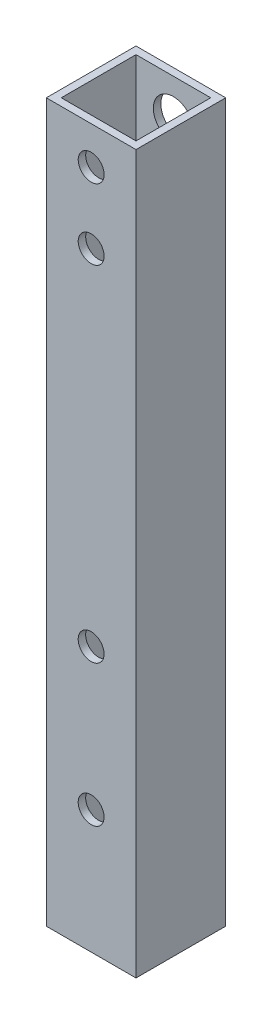
SolidWorks part; units mm, degrees
material "6063-T5"
ref_plane "Front Plane" through (0, 0, 0) normal (0, 0, 1) x (1, 0, 0)
ref_plane "Top Plane" through (0, 0, 0) normal (0, 1, 0) x (1, 0, 0)
ref_plane "Right Plane" through (0, 0, 0) normal (1, 0, 0) x (0, 0, -1)
sketch "Sketch1" plane through (0, 0, 0) normal (0, 1, 0) x (1, 0, 0)
  line L0 (1.5875, 1.5875) -> (17.4625, 1.5875)
  line L5 (0, 0) -> (19.05, 0)
  line L6 (0, 0) -> (0, 19.05)
  line L7 (0, 19.05) -> (19.05, 19.05)
  line L8 (19.05, 0) -> (19.05, 19.05)
  line L9 (17.4625, 1.5875) -> (17.4625, 17.4625)
  line L10 (1.5875, 17.4625) -> (17.4625, 17.4625)
  line L11 (1.5875, 1.5875) -> (1.5875, 17.4625)
  dimension "D1" = 19.05
  dimension "D2" = 19.05
  dimension "D3" = 1.5875
extrude "Boss-Extrude1" add sketch "Sketch1" along normal blind 914.4
sketch "Sketch2" plane through (0, 0, 0) normal (0, 0, 1) x (1, 0, 0)
  line L0 (0, 914.4) -> (19.05, 914.4) construction
  circle A0 centre (9.525, 906.4) radius 2.75
  circle A1 centre (9.525, 891.4) radius 2.75
  dimension "D3" = 5.5
  dimension "D4" = 5.5
  dimension "D1" = 8
  dimension "D2" = 15
extrude "Cut-Extrude1" cut sketch "Sketch2" against normal through all
sketch "Sketch3" plane through (0, 0, -19.05) normal (0, 0, -1) x (-1, 0, 0)
  circle A0 centre (-9.525, 906.4) radius 4.255
  circle A1 centre (-9.525, 891.4) radius 4.255
  dimension "D1" = 8.51
  dimension "D2" = 8.51
extrude "Cut-Extrude2" cut sketch "Sketch3" against normal up to next
sketch "Sketch4" plane through (0, 0, 0) normal (0, 0, 1) x (1, 0, 0)
  line L0 (19.05, 914.4) -> (19.05, 0) construction
  line L1 (0, 0) -> (19.05, 0)
  line L2 (0, 0) -> (0, 762)
  line L3 (0, 762) -> (19.05, 762)
  line L4 (19.05, 0) -> (19.05, 762)
  line L5 (0, 914.4) -> (19.05, 914.4) construction
  dimension "D1" = 152.4
extrude "Cut-Extrude3" cut sketch "Sketch4" against normal through all
sketch "Sketch5" plane through (0, 0, 0) normal (0, 0, 1) x (1, 0, 0)
  line L0 (19.05, 762) -> (0, 762) construction
  line L1 (19.05, 914.4) -> (19.05, 762) construction
  circle A0 centre (9.52, 788.2) radius 2.75
  circle A1 centre (9.52, 818.2) radius 2.75
  dimension "D1" = 5.5
  dimension "D2" = 5.5
  dimension "D3" = 26.2
  dimension "D4" = 56.2
  dimension "D5" = 9.53
  dimension "D6" = 9.53
extrude "Cut-Extrude4" cut sketch "Sketch5" against normal through all
